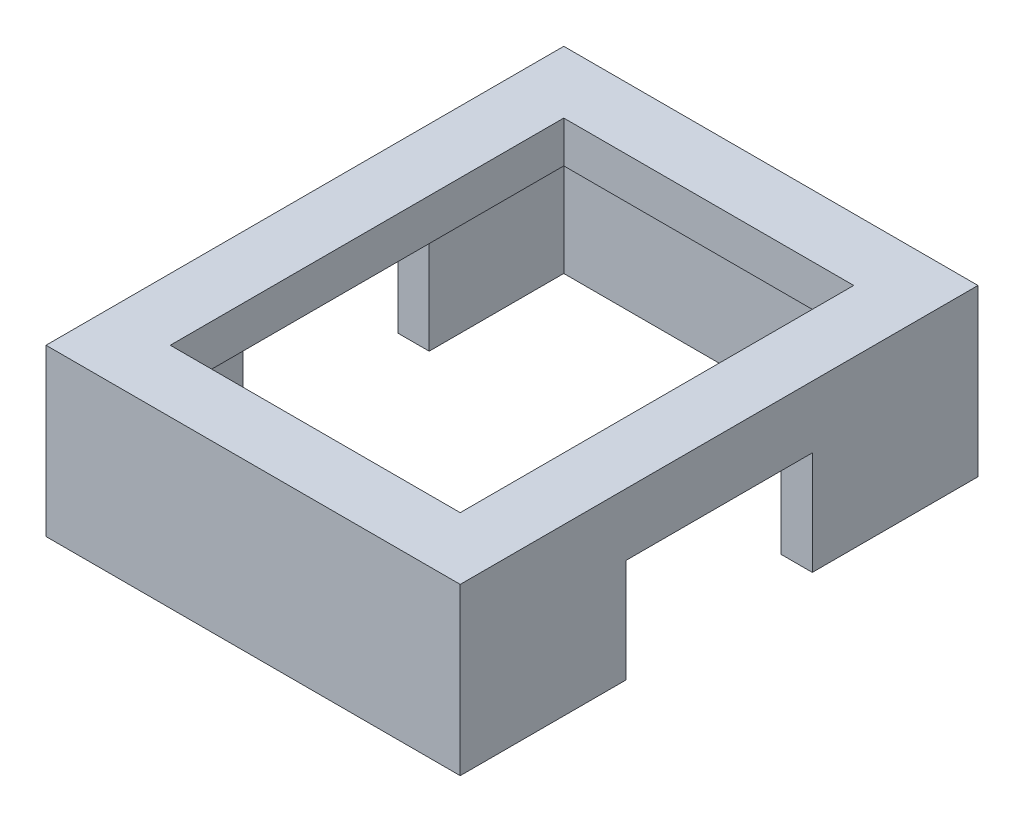
SolidWorks part; units mm, degrees
ref_plane "Front Plane" through (0, 0, 0) normal (0, 0, 1) x (1, 0, 0)
ref_plane "Top Plane" through (0, 0, 0) normal (0, 1, 0) x (1, 0, 0)
ref_plane "Right Plane" through (0, 0, 0) normal (1, 0, 0) x (0, 0, -1)
sketch "Sketch1" plane through (0, 0, 0) normal (0, 1, 0) x (1, 0, 0)
  line L1 (-20.9032, 9.871) -> (-0.9032, 9.871)
  line L2 (-20.9032, 9.871) -> (-20.9032, -15.129)
  line L3 (-20.9032, -15.129) -> (-0.9032, -15.129)
  line L4 (-0.9032, 9.871) -> (-0.9032, -15.129)
  dimension "D1" = 20
  dimension "D2" = 25
extrude "Boss-Extrude1" add sketch "Sketch1" along normal blind 8
sketch "Sketch2" plane through (-20.9032, 0, 0) normal (-1, 0, 0) x (0, 0, 1)
  line L0 (-9.871, 0) -> (15.129, 0) construction
  line L1 (-1.871, 5) -> (7.129, 5)
  line L2 (-1.871, 5) -> (-1.871, 0)
  line L3 (-1.871, 0) -> (7.129, 0)
  line L4 (7.129, 5) -> (7.129, 0)
  line L8 (-9.871, 8) -> (-9.871, 0) construction
  dimension "D1" = 5
  dimension "D2" = 9
  dimension "D3" = 8
extrude "Cut-Extrude1" cut sketch "Sketch2" against normal blind 31
sketch "Sketch3" plane through (0, 0, 0) normal (0, -1, 0) x (1, 0, 0)
  line L1 (-2.4032, -8.371) -> (-19.4032, -8.371)
  line L2 (-2.4032, -8.371) -> (-2.4032, 13.629)
  line L3 (-2.4032, 13.629) -> (-19.4032, 13.629)
  line L4 (-19.4032, -8.371) -> (-19.4032, 13.629)
  line L6 (-0.9032, -9.871) -> (-20.9032, -9.871) construction
  line L8 (-20.9032, -9.871) -> (-20.9032, 15.129) construction
  line L9 (-0.9032, -1.871) -> (-0.9032, -9.871) construction
  line L10 (-20.9032, 15.129) -> (-0.9032, 15.129) construction
  dimension "D3" = 1.5
  dimension "D2" = 1.5
  dimension "D1" = 1.5
  dimension "D4" = 1.5
extrude "Cut-Extrude2" cut sketch "Sketch3" against normal blind 6
sketch "Sketch4" plane through (0, 8, 0) normal (0, 1, 0) x (1, 0, 0)
  line L1 (-17.9032, 6.871) -> (-3.9032, 6.871)
  line L2 (-17.9032, 6.871) -> (-17.9032, -12.129)
  line L3 (-17.9032, -12.129) -> (-3.9032, -12.129)
  line L4 (-3.9032, 6.871) -> (-3.9032, -12.129)
  line L5 (-0.9032, 9.871) -> (-20.9032, 9.871) construction
  line L6 (-0.9032, -15.129) -> (-0.9032, 9.871) construction
  line L7 (-20.9032, -15.129) -> (-0.9032, -15.129) construction
  line L8 (-20.9032, 9.871) -> (-20.9032, -15.129) construction
  dimension "D2" = 3
  dimension "D3" = 3
  dimension "D4" = 3
  dimension "D1" = 3
extrude "Cut-Extrude3" cut sketch "Sketch4" against normal blind 7
equation "\"buckle_thickness\"= 8"
equation "\"visable_border\"= 3"
equation "\"cutout_border\"= 1.5"
equation "\"belt_thickness\"= 9"
equation "\"belt_width\"= 5"
equation "\"D1@belt_cutout\" = \"belt_thickness\""
equation "\"D2@belt_cutout\" = \"belt_width\""
equation "\"belt_placement\"= 7.5"
equation "\"D3@belt_cutout\" = \"belt_placement\""
equation "\"D1@cutout\" = \"cutout_border\""
equation "\"D2@cutout\" = \"cutout_border\""
equation "\"D3@cutout\" = \"cutout_border\""
equation "\"D4@cutout\" = \"cutout_border\""
equation "\"D5@cutout\" = \"cutout_border\""
equation "\"D4@Sketch2\"=\"visable_border\""
equation "\"D6@Sketch2\"=\"visable_border\""
equation "\"base_size\"= 30"
equation "\"D2@Sketch3\"=\"cutout_border\""
equation "\"D3@Sketch3\"=\"cutout_border\""
equation "\"D1@Sketch3\"=\"cutout_border\""
equation "\"D4@Sketch3\"=\"cutout_border\""
equation "\"D3@Sketch4\"=\"visable_border\""
equation "\"D2@Sketch4\"=\"visable_border\""
equation "\"D4@Sketch4\"=\"visable_border\""
equation "\"D1@Sketch4\"=\"visable_border\""
equation "\"D1@Sketch2\"=\"belt_width\""
equation "\"D2@Sketch2\"=\"belt_thickness\""
equation "\"middle_buckle_width\"= 20"
equation "\"D1@Sketch1\"=\"middle_buckle_width\""
equation "\"middle_buckle_height\"= 25"
equation "\"D2@Sketch1\"=\"middle_buckle_height\""
equation "\"D3@Sketch2\"= \"middle_buckle_height\"/2 - \"belt_thickness\"/2"
